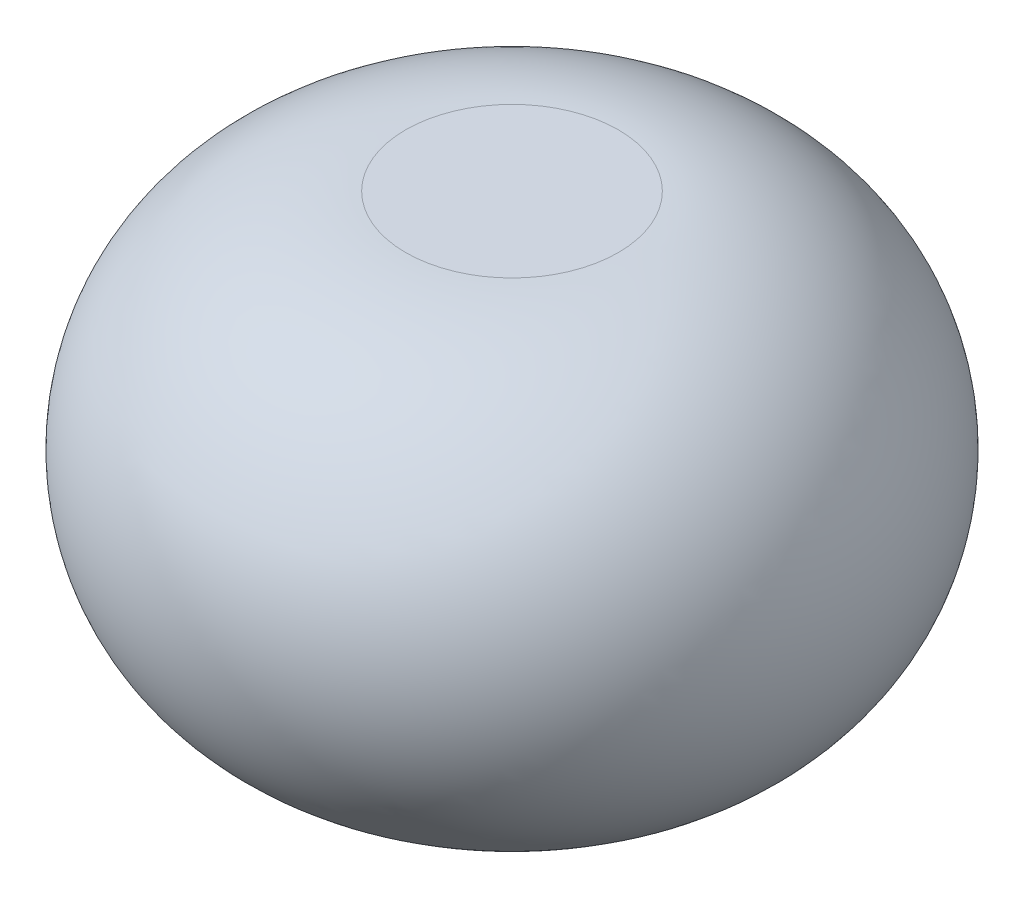
SolidWorks part; units mm, degrees
ref_plane "Płaszczyzna przednia" through (0, 0, 0) normal (0, 0, 1) x (1, 0, 0)
ref_plane "Płaszczyzna górna" through (0, 0, 0) normal (0, 1, 0) x (1, 0, 0)
ref_plane "Płaszczyzna prawa" through (0, 0, 0) normal (1, 0, 0) x (0, 0, -1)
sketch "Szkic2" plane through (0, 0, 0) normal (0, 0, 1) x (1, 0, 0)
  line L0 (0, 0) -> (0, 4200) construction
  line L1 (0, 4200) -> (1000, 4200)
  line L2 (0, 0) -> (1000, 0)
  arc A0 (1000, 4200) -> (1000, 0) centre (1000, 2100) cw
  dimension "D2" = 1000
  dimension "D1" = 4200
  dimension "D3" = 1000
revolve "Obrót-cienka ścianka1" add sketch "Szkic2" angle 360 about L0
